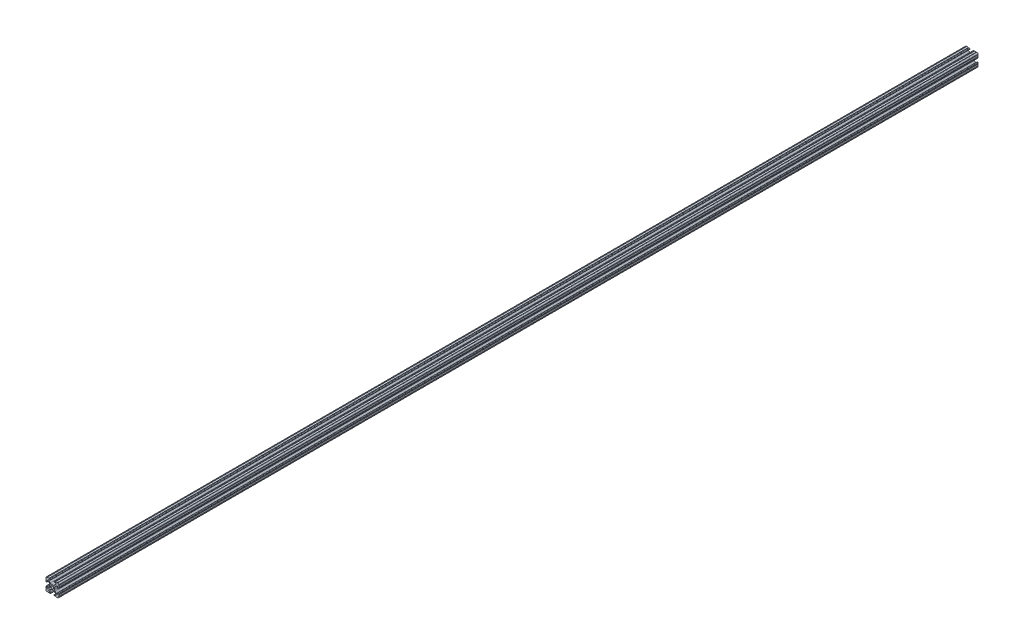
SolidWorks part; units mm, degrees
ref_plane "Front Plane" through (0, 0, 0) normal (0, 0, 1) x (1, 0, 0)
ref_plane "Top Plane" through (0, 0, 0) normal (0, 1, 0) x (1, 0, 0)
ref_plane "Right Plane" through (0, 0, 0) normal (1, 0, 0) x (0, 0, -1)
sketch "Sketch1" plane through (0, 0, 0) normal (0, 0, 1) x (1, 0, 0)
  line L88 (-7.1797, -8.6452) -> (-3.9523, -5.4237)
  line L89 (-1.7093, -4.4958) -> (1.7093, -4.4958)
  line L90 (3.9523, -5.4237) -> (7.1797, -8.6452)
  line L91 (6.4164, -10.4902) -> (4.2875, -10.4902)
  line L92 (3.2385, -11.5392) -> (3.2385, -11.651)
  line L93 (4.2875, -12.7) -> (5.3171, -12.7)
  line L94 (6.3331, -12.7) -> (9.5504, -12.7)
  line L95 (12.7, -9.5504) -> (12.7, -6.3331)
  line L96 (12.7, -5.3171) -> (12.7, -4.2875)
  line L97 (11.651, -3.2385) -> (11.5392, -3.2385)
  line L98 (10.4902, -4.2875) -> (10.4902, -6.4021)
  line L99 (8.7371, -7.1294) -> (5.441, -3.8408)
  line L100 (4.5085, -1.5932) -> (4.5085, 1.5932)
  line L101 (5.441, 3.8408) -> (8.7371, 7.1294)
  line L102 (10.4902, 6.4021) -> (10.4902, 4.2875)
  line L103 (11.5392, 3.2385) -> (11.651, 3.2385)
  line L104 (12.7, 4.2875) -> (12.7, 5.3171)
  line L105 (12.7, 6.3331) -> (12.7, 9.5504)
  line L106 (9.5504, 12.7) -> (6.3331, 12.7)
  line L107 (5.3171, 12.7) -> (4.2875, 12.7)
  line L108 (3.2385, 11.651) -> (3.2385, 11.5392)
  line L109 (4.2875, 10.4902) -> (6.4768, 10.4902)
  line L110 (7.207, 8.7244) -> (3.8983, 5.4232)
  line L111 (1.6558, 4.4958) -> (-1.6558, 4.4958)
  line L112 (-3.8983, 5.4232) -> (-7.207, 8.7244)
  line L113 (-6.4768, 10.4902) -> (-4.2875, 10.4902)
  line L114 (-3.2385, 11.5392) -> (-3.2385, 11.651)
  line L115 (-4.2875, 12.7) -> (-5.3171, 12.7)
  line L116 (-6.3331, 12.7) -> (-9.5504, 12.7)
  line L117 (-12.7, 9.5504) -> (-12.7, 6.3331)
  line L118 (-12.7, 5.3171) -> (-12.7, 4.2875)
  line L119 (-11.651, 3.2385) -> (-11.5392, 3.2385)
  line L120 (-10.4902, 4.2875) -> (-10.4902, 6.4021)
  line L121 (-8.7371, 7.1294) -> (-5.441, 3.8408)
  line L122 (-4.5085, 1.5932) -> (-4.5085, -1.5932)
  line L123 (-5.441, -3.8408) -> (-8.7371, -7.1294)
  line L124 (-10.4902, -6.4021) -> (-10.4902, -4.2875)
  line L125 (-11.5392, -3.2385) -> (-11.651, -3.2385)
  line L126 (-12.7, -4.2875) -> (-12.7, -5.3171)
  line L127 (-12.7, -6.3331) -> (-12.7, -9.5504)
  line L128 (-9.5504, -12.7) -> (-6.3331, -12.7)
  line L129 (-5.3171, -12.7) -> (-4.2875, -12.7)
  line L130 (-3.2385, -11.651) -> (-3.2385, -11.5392)
  line L131 (-4.2875, -10.4902) -> (-6.4164, -10.4902)
  circle A1 centre (0, 0) radius 2.6035
  arc A104 (-7.1797, -8.6452) -> (-6.4164, -10.4902) centre (-6.4164, -9.4098) ccw
  arc A105 (-1.7093, -4.4958) -> (-3.9523, -5.4237) centre (-1.7093, -7.6708) ccw
  arc A106 (3.9523, -5.4237) -> (1.7093, -4.4958) centre (1.7093, -7.6708) ccw
  arc A107 (6.4164, -10.4902) -> (7.1797, -8.6452) centre (6.4164, -9.4098) ccw
  arc A108 (4.2875, -10.4902) -> (3.2385, -11.5392) centre (4.2875, -11.5392) ccw
  arc A109 (3.2385, -11.651) -> (4.2875, -12.7) centre (4.2875, -11.651) ccw
  arc A110 (6.3331, -12.7) -> (5.3171, -12.7) centre (5.8251, -12.7) ccw
  arc A111 (10.5664, -12.6998) -> (9.5504, -12.7) centre (10.0584, -12.7) ccw
  arc A112 (10.5664, -12.6998) -> (12.6998, -10.5664) centre (10.5918, -10.5918) ccw
  arc A113 (12.7, -9.5504) -> (12.6998, -10.5664) centre (12.7, -10.0584) ccw
  arc A114 (12.7, -5.3171) -> (12.7, -6.3331) centre (12.7, -5.8251) ccw
  arc A115 (12.7, -4.2875) -> (11.651, -3.2385) centre (11.651, -4.2875) ccw
  arc A116 (11.5392, -3.2385) -> (10.4902, -4.2875) centre (11.5392, -4.2875) ccw
  arc A117 (8.7371, -7.1294) -> (10.4902, -6.4021) centre (9.4628, -6.4021) ccw
  arc A118 (4.5085, -1.5932) -> (5.441, -3.8408) centre (7.6835, -1.5932) ccw
  arc A119 (5.441, 3.8408) -> (4.5085, 1.5932) centre (7.6835, 1.5932) ccw
  arc A120 (10.4902, 6.4021) -> (8.7371, 7.1294) centre (9.4628, 6.4021) ccw
  arc A121 (10.4902, 4.2875) -> (11.5392, 3.2385) centre (11.5392, 4.2875) ccw
  arc A122 (11.651, 3.2385) -> (12.7, 4.2875) centre (11.651, 4.2875) ccw
  arc A123 (12.7, 6.3331) -> (12.7, 5.3171) centre (12.7, 5.8251) ccw
  arc A124 (12.6998, 10.5664) -> (12.7, 9.5504) centre (12.7, 10.0584) ccw
  arc A125 (12.6998, 10.5664) -> (10.5664, 12.6998) centre (10.5918, 10.5918) ccw
  arc A126 (9.5504, 12.7) -> (10.5664, 12.6998) centre (10.0584, 12.7) ccw
  arc A127 (5.3171, 12.7) -> (6.3331, 12.7) centre (5.8251, 12.7) ccw
  arc A128 (4.2875, 12.7) -> (3.2385, 11.651) centre (4.2875, 11.651) ccw
  arc A129 (3.2385, 11.5392) -> (4.2875, 10.4902) centre (4.2875, 11.5392) ccw
  arc A130 (7.207, 8.7244) -> (6.4768, 10.4902) centre (6.4768, 9.4563) ccw
  arc A131 (1.6558, 4.4958) -> (3.8983, 5.4232) centre (1.6558, 7.6708) ccw
  arc A132 (-3.8983, 5.4232) -> (-1.6558, 4.4958) centre (-1.6558, 7.6708) ccw
  arc A133 (-6.4768, 10.4902) -> (-7.207, 8.7244) centre (-6.4768, 9.4563) ccw
  arc A134 (-4.2875, 10.4902) -> (-3.2385, 11.5392) centre (-4.2875, 11.5392) ccw
  arc A135 (-3.2385, 11.651) -> (-4.2875, 12.7) centre (-4.2875, 11.651) ccw
  arc A136 (-6.3331, 12.7) -> (-5.3171, 12.7) centre (-5.8251, 12.7) ccw
  arc A137 (-10.5664, 12.6998) -> (-9.5504, 12.7) centre (-10.0584, 12.7) ccw
  arc A138 (-10.5664, 12.6998) -> (-12.6998, 10.5664) centre (-10.5918, 10.5918) ccw
  arc A139 (-12.7, 9.5504) -> (-12.6998, 10.5664) centre (-12.7, 10.0584) ccw
  arc A140 (-12.7, 5.3171) -> (-12.7, 6.3331) centre (-12.7, 5.8251) ccw
  arc A141 (-12.7, 4.2875) -> (-11.651, 3.2385) centre (-11.651, 4.2875) ccw
  arc A142 (-11.5392, 3.2385) -> (-10.4902, 4.2875) centre (-11.5392, 4.2875) ccw
  arc A143 (-8.7371, 7.1294) -> (-10.4902, 6.4021) centre (-9.4628, 6.4021) ccw
  arc A144 (-4.5085, 1.5932) -> (-5.441, 3.8408) centre (-7.6835, 1.5932) ccw
  arc A145 (-5.441, -3.8408) -> (-4.5085, -1.5932) centre (-7.6835, -1.5932) ccw
  arc A146 (-10.4902, -6.4021) -> (-8.7371, -7.1294) centre (-9.4628, -6.4021) ccw
  arc A147 (-10.4902, -4.2875) -> (-11.5392, -3.2385) centre (-11.5392, -4.2875) ccw
  arc A148 (-11.651, -3.2385) -> (-12.7, -4.2875) centre (-11.651, -4.2875) ccw
  arc A149 (-12.7, -6.3331) -> (-12.7, -5.3171) centre (-12.7, -5.8251) ccw
  arc A150 (-12.6998, -10.5664) -> (-12.7, -9.5504) centre (-12.7, -10.0584) ccw
  arc A151 (-12.6998, -10.5664) -> (-10.5664, -12.6998) centre (-10.5918, -10.5918) ccw
  arc A152 (-9.5504, -12.7) -> (-10.5664, -12.6998) centre (-10.0584, -12.7) ccw
  arc A153 (-5.3171, -12.7) -> (-6.3331, -12.7) centre (-5.8251, -12.7) ccw
  arc A154 (-4.2875, -12.7) -> (-3.2385, -11.651) centre (-4.2875, -11.651) ccw
  arc A155 (-3.2385, -11.5392) -> (-4.2875, -10.4902) centre (-4.2875, -11.5392) ccw
extrude "Boss-Extrude1" add sketch "Sketch1" along normal mid plane 1828.8
